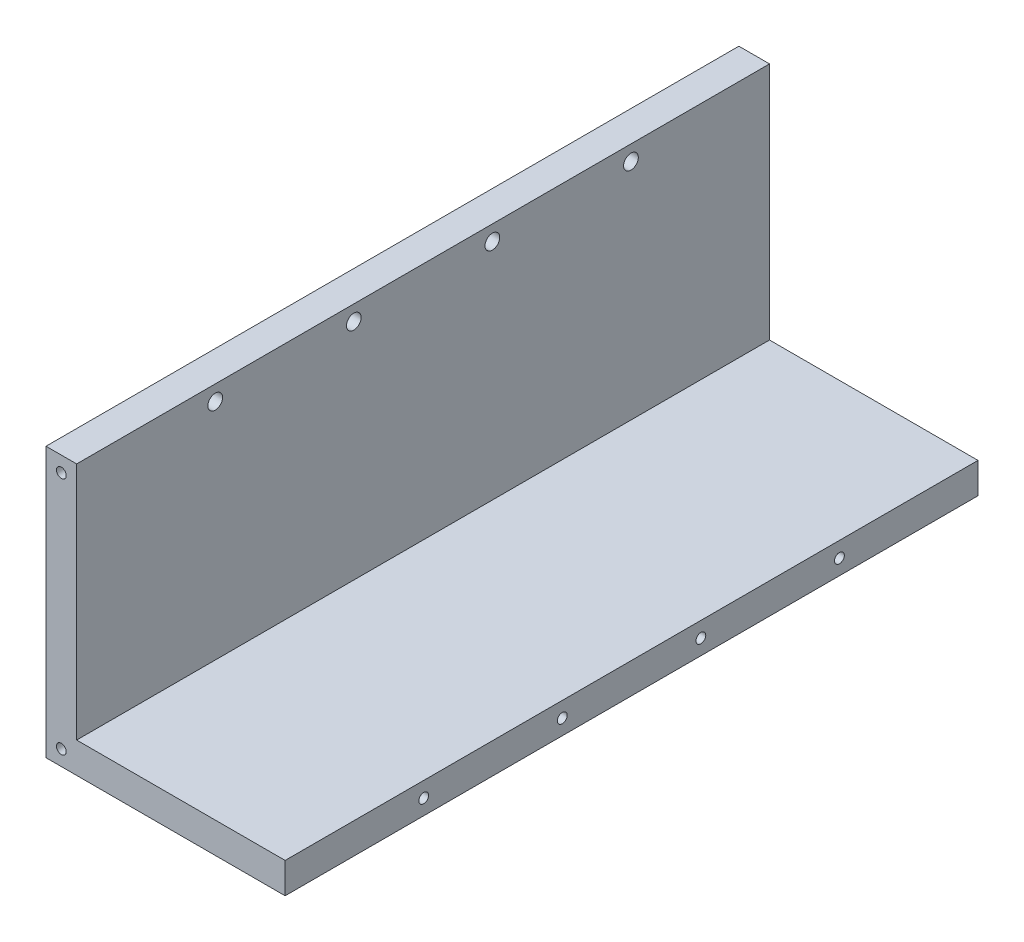
SolidWorks part; units mm, degrees
ref_plane "Plan de face" through (0, 0, 0) normal (1, 0, 0) x (0, 1, 0)
ref_plane "Plan de dessus" through (0, 0, 0) normal (0, 0, 1) x (0, 1, 0)
ref_plane "Plan de droite" through (0, 0, 0) normal (0, 1, 0) x (-1, 0, 0)
sketch "Esquisse1" plane through (0, 0, 0) normal (0, 0, 1) x (0, 1, 0)
  line L0 (0, 0) -> (39, 0)
  line L2 (0, 0) -> (0, -34)
  line L3 (0, -34) -> (-5, -34)
  line L4 (-5, 0) -> (-5, -34)
  line L6 (-5, 0) -> (-5, 5)
  line L7 (-5, 5) -> (39, 5)
  line L8 (39, 0) -> (39, 5)
extrude "Boss_Extrude_Equerre" add sketch "Esquisse1" along normal blind 113
hole_wizard "Fraisage pour vis à tête fraisée M20" positions "Esquisse6" profile "Esquisse3" countersink size "M2" standard "Ansi Metric"
sketch "Esquisse6" plane through (-5, 0, 0) normal (-1, 0, 0) x (0, 0, 1)
  line L2 (113, 39) -> (113, -5) construction
  line L3 (0, 36.5) -> (113, 36.5) construction
  line L4 (0, 39) -> (0, -5) construction
  line L5 (113, -5) -> (0, -5) construction
  point P0 (67.8, 36.5)
  point P2 (90.4, 36.5)
  point P10 (45.2, 36.5)
  point P12 (22.6, 36.5)
  dimension "D5" = 22.6
  dimension "D6" = 22.6
  dimension "D1" = 22.6
sketch "Esquisse3" plane through (-5, 36.5, 67.8) normal (0, 1, 0) x (0, 0, 1)
  line L0 (0, 0) -> (0, 5.721)
  line L1 (0, 5.721) -> (1.2, 5)
  line L2 (1.2, 5) -> (1.2, 1)
  line L3 (1.2, 1) -> (2.2, 0)
  line L5 (2.2, 0) -> (0, 0)
  line L6 (-1.2, 1) -> (-2.2, 0) construction
  line L10 (0, 5.721) -> (-1.2, 5) construction
  line L11 (0, -6.35) -> (0, 107.95) construction
  dimension "Diamètre du perçage" = 2.4
  dimension "Profondeur du perçage" = 5
  dimension "Diamètre du fraisage entrant" = 4.4
  dimension "Angle du fraisage entrant" = 90
  dimension "Angle de pointe" = 118
hole_wizard "Trou taraudé M2x0.43" positions "Esquisse7" profile "Esquisse8" tap size "M2x0.4" standard "Ansi Metric"
sketch "Esquisse7" plane through (34, 0, 0) normal (1, 0, 0) x (0, 1, 0)
  line L1 (-5, 0) -> (0, 0) construction
  line L4 (-2.5, 0) -> (-2.5, 113) construction
  line L5 (-5, 113) -> (0, 113) construction
  point P0 (-2.5, 67.8)
  point P2 (-2.5, 90.4)
  point P13 (-2.5, 45.2)
  point P15 (-2.5, 22.6)
  dimension "D5" = 22.6
  dimension "D1" = 22.6
  dimension "D3" = 22.6
  dimension "D4" = 22.6
cosmetic thread "Filetage de perçage1" parameters "D1"=8, "D2"=2
cosmetic thread "Filetage de perçage2" parameters "D1"=8, "D2"=2
cosmetic thread "Filetage de perçage3" parameters "D1"=8, "D2"=2
cosmetic thread "Filetage de perçage4" parameters "D1"=8, "D2"=2
sketch "Esquisse8" plane through (34, -2.5, 67.8) normal (0, 1, 0) x (0, 0, -1)
  line L0 (0, 0) -> (0, 8.4807)
  line L1 (0, 8.4807) -> (0.8, 8)
  line L2 (0.8, 8) -> (0.8, 0)
  line L5 (0.8, 0) -> (0, 0)
  line L10 (0, 8.4807) -> (-0.8, 8) construction
  line L11 (0, -6.35) -> (0, 107.95) construction
  dimension "Diamètre du trou pour taraudage" = 1.6
  dimension "Profondeur du trou pour taraudage" = 8
  dimension "Angle de pointe" = 118
hole_wizard "Trou taraudé M2x0.44" positions "Esquisse9" profile "Esquisse11" tap size "M2x0.4" standard "Ansi Metric"
sketch "Esquisse9" plane through (0, 0, 113) normal (0, 0, 1) x (1, 0, 0)
  line L0 (-2.5, 39) -> (-2.5, -5) construction
  line L1 (0, 39) -> (-5, 39) construction
  line L2 (-5, -5) -> (34, -5) construction
  line L3 (0, 36.5) -> (-7.2751, 36.5) construction
  line L4 (0, 0) -> (0, 39) construction
  line L12 (-5, -2.5) -> (34, -2.5) construction
  line L13 (-5, 39) -> (-5, -5) construction
  line L14 (34, -5) -> (34, 0) construction
  point P0 (-2.5, 36.5)
  point P2 (-2.5, -2.5)
  dimension "D1" = 2.5
cosmetic thread "Filetage de perçage6" parameters "D1"=8, "D2"=2
cosmetic thread "Filetage de perçage7" parameters "D1"=8, "D2"=2
sketch "Esquisse11" plane through (-2.5, 36.5, 113) normal (1, 0, 0) x (0, -1, 0)
  line L0 (0, 0) -> (0, 8.4807)
  line L1 (0, 8.4807) -> (0.8, 8)
  line L2 (0.8, 8) -> (0.8, 0)
  line L5 (0.8, 0) -> (0, 0)
  line L10 (0, 8.4807) -> (-0.8, 8) construction
  line L11 (0, -6.35) -> (0, 107.95) construction
  dimension "Diamètre du trou pour taraudage" = 1.6
  dimension "Profondeur du trou pour taraudage" = 8
  dimension "Angle de pointe" = 118
ref_plane "Plan1" through (0, 0, 56.5) normal (0, 0, 1) x (1, 0, 0)
mirror "Symétrie1" about plane through (0, 0, 56.5) normal (0, 0, 1) of "Trou taraudé M2x0.44"
cosmetic thread "Filetage de perçage8" parameters "D1"=8, "D2"=2
cosmetic thread "Filetage de perçage9" parameters "D1"=8, "D2"=2
equation "\"Plaque_L\"=\"Cavite_L\"+\"Cavite_E\"'longueur plaque"
equation "\"Plaque_H\"= \"Cavite_L\"+\"Cavite_E\"'largeur plaque"
equation "\"Plaque_E\"= 2mm'épaisseur plaque superieure et inferieure"
equation "\"Trou_R\"= 1.2mm'rayon perforation base"
equation "\"Trou_dx\"= 4mm'distance entre trou sur x"
equation "\"Trou-dy\"= 4mm'distance entre trou sur y"
equation "\"Cavite_H\"= 18mm'hauteur cavité"
equation "\"Cavite_L\"=\"Cavite_largeur\"+\"Cavite_E\"'longueur cavité"
equation "\"Cavite_E\"= 3mm'épaisseur cavité"
equation "\"Offset_Z\"= 0mm"
equation "\"D2@Esquisse1\"=\"Enveloppe_E\""
equation "\"D3@Esquisse1\"=\"Longueur_equerre_enveloppe\""
equation "\"D1@Esquisse1\"=\"Largeur_equerre_enveloppe\""
equation "\"Vis_Diam\"= 1.6mm"
equation "\"Offset_Bord\"= \"Cavite_E\" / 2"
equation "\"Vis_Long\"= 5mm"
equation "\"Perc_Passage\"= 1.8mm"
equation "\"Perc_Taraud\"= 1.3mm"
equation "\"Fraisure_Diam\"= 3mm"
equation "\"Fraisure_Prof\"= 1mm"
equation "\"Offset_hauteur_vis1\"= \"Cavite_E\""
equation "\"Offset_hauteur_vis2\"= \"Cavite_H\" - \"Cavite_E\""
equation "\"Perc_Profondeur\"= 8mm"
equation "\"Taraud_Profondeur\"= \"Cavite_E\""
equation "\"Cavite_largeur\"= 28mm'largeur cavité"
equation "\"D1@Boss_Extrude_Equerre\"=\"H_total\""
equation "\"H_total\"=113mm'122-2*2"
equation "\"espace_trou\"= 22.6mm"
equation "\"D5@Esquisse6\"=\"espace_vis\""
equation "\"D6@Esquisse6\"=\"espace_vis\""
equation "\"D2@Esquisse6\"=\"espace_vis\""
equation "\"D3@Esquisse7\"=\"espace_vis\""
equation "\"D4@Esquisse7\"=\"espace_vis\""
equation "\"D5@Esquisse7\"=\"espace_vis\""
equation "\"D1@Esquisse9\"=\"Offset_Enveloppe\""
equation "\"D2@Esquisse9\"=\"Offset_Enveloppe\""
equation "\"espace_vis\"=22.6mm'"
equation "\"Enveloppe_E\"=5mm"
equation "\"Offset_cavite\"= \"Cavite_E\" / 2"
equation "\"Offset_Enveloppe\"= \"Enveloppe_E\" / 2"
equation "\"D3@Esquisse6\"=\"Longueur_equerre_enveloppe\"+\"Enveloppe_E\"-\"Offset_Enveloppe\""
equation "\"Largeur_enveloppe\"=\"Cavite_largeur\"+\"Cavite_E\""
equation "\"Longueur_enveloppe\"=\"Cavite_L\"+\"Enveloppe_E\""
equation "\"N_Plaque\"= 7"
equation "\"N_Cavite\"= 6"
equation "\"Largeur_equerre_enveloppe\"=\"Cavite_L\"+\"Cavite_E\""
equation "\"Longueur_equerre_enveloppe\"=\"Cavite_L\"+\"Cavite_E\"+\"Enveloppe_E\""
equation "\"largeur_plaque_enveloppe\"=\"Longueur_equerre_enveloppe\"+\"Enveloppe_E\""
equation "\"D1@Esquisse6\"=\"espace_vis\""
equation "\"D1@Esquisse7\"=\"espace_vis\""
